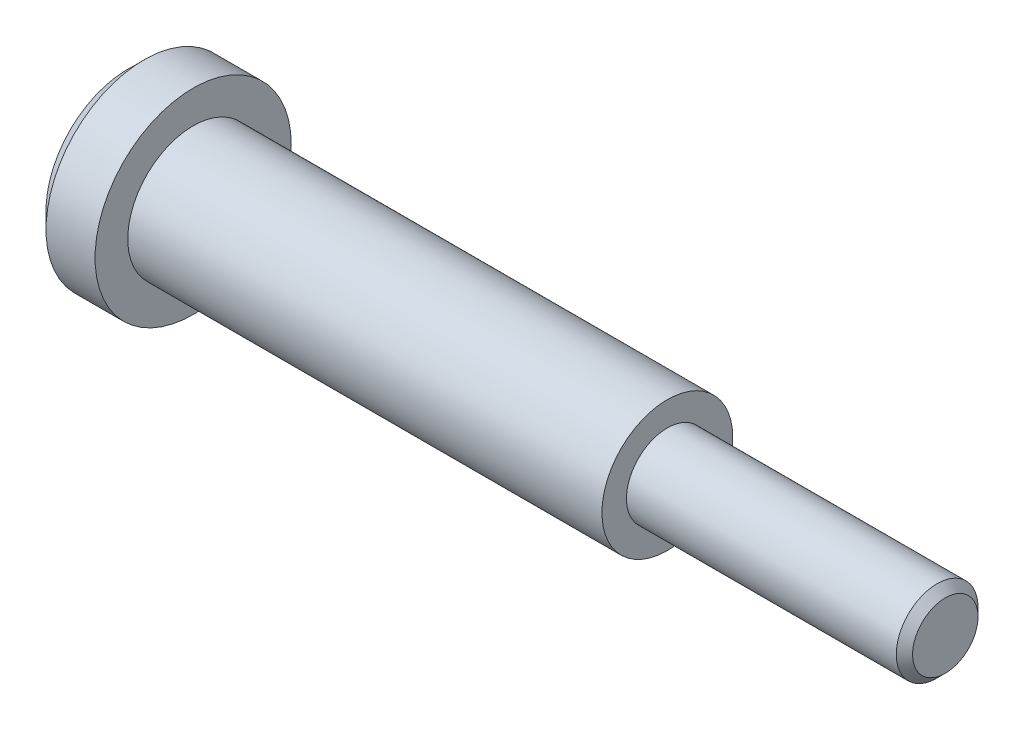
SolidWorks part; units mm, degrees
ref_plane "Front Plane" through (0, 0, 0) normal (0, 0, 1) x (1, 0, 0)
ref_plane "Top Plane" through (0, 0, 0) normal (0, 1, 0) x (1, 0, 0)
ref_plane "Right Plane" through (0, 0, 0) normal (1, 0, 0) x (0, 0, -1)
sketch "Sketch1" plane through (0, 0, 0) normal (1, 0, 0) x (0, 0, -1)
  circle A0 centre (0, 0) radius 6
  dimension "D1" = 12
extrude "Boss-Extrude1" add sketch "Sketch1" along normal blind 4
sketch "Sketch2" plane through (4, 0, 0) normal (1, 0, 0) x (0, 0, -1)
  circle A0 centre (0, 0) radius 4
  dimension "D1" = 8
extrude "Boss-Extrude2" add sketch "Sketch2" along normal blind 29
sketch "Sketch3" plane through (33, 0, 0) normal (1, 0, 0) x (0, 0, -1)
  circle A0 centre (0, 0) radius 2.5
  dimension "D1" = 5
extrude "Boss-Extrude3" add sketch "Sketch3" along normal blind 17
chamfer "Chamfer1" distance 0.5 angle 45 1 edges at (50, 0, -2.5)
chamfer "Chamfer2" distance 1 angle 45 1 edges at (0, 0, -6)
sketch "Sketch4" plane through (0, 0, 0) normal (-1, 0, 0) x (0, 0, 1)
  circle A0 centre (0, 0) radius 2.5
  dimension "D1" = 5
extrude "Cut-Extrude1" cut sketch "Sketch4" against normal blind 1
fillet "Fillet1" radius 0.5 1 edges at (0, 0, 2.5)
